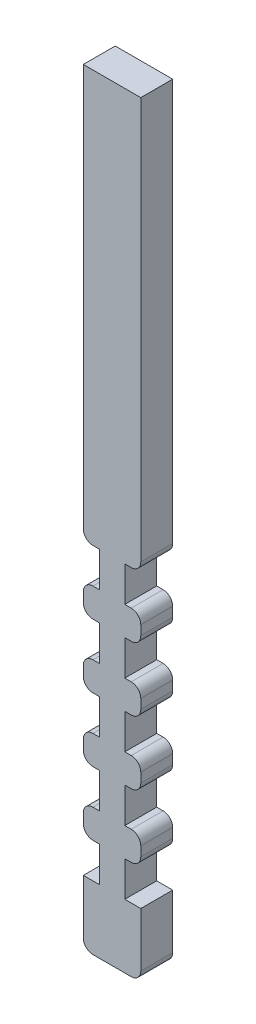
SolidWorks part; units mm, degrees
ref_plane "Front Plane" through (0, 0, 0) normal (0, 0, 1) x (1, 0, 0)
ref_plane "Top Plane" through (0, 0, 0) normal (0, 1, 0) x (1, 0, 0)
ref_plane "Right Plane" through (0, 0, 0) normal (1, 0, 0) x (0, 0, -1)
sketch "Sketch1" plane through (0, 0, 0) normal (0, 0, 1) x (1, 0, 0)
  line L0 (0, 120) -> (0, 0) construction
  line L1 (-9, 0) -> (9, 0)
  line L2 (-9, 0) -> (-9, 120) construction
  line L3 (-9, 120) -> (9, 120) construction
  line L5 (-9, 120) -> (-9, 111)
  line L6 (-9, 111) -> (-3.99, 111)
  line L7 (-3.99, 111) -> (-3.99, 100)
  line L8 (-3.99, 100) -> (-9, 100)
  line L9 (-9, 100) -> (-9, 91)
  line L10 (-9, 91) -> (-3.99, 91)
  line L11 (-3.99, 91) -> (-3.99, 80)
  line L12 (-3.99, 80) -> (-9, 80)
  line L13 (-9, 80) -> (-9, 71)
  line L14 (-9, 71) -> (-3.99, 71)
  line L15 (-3.99, 71) -> (-3.99, 60)
  line L16 (-3.99, 60) -> (-9, 60)
  line L17 (-9, 60) -> (-9, 51)
  line L18 (-9, 51) -> (-3.99, 51)
  line L19 (-3.99, 51) -> (-3.99, 40)
  line L20 (-3.99, 40) -> (-9, 40)
  line L21 (-9, 40) -> (-9, 31)
  line L22 (-9, 31) -> (-3.99, 31)
  line L23 (-3.99, 31) -> (-3.99, 20)
  line L24 (-3.99, 20) -> (-9, 20)
  line L25 (-9, 0) -> (-9, 20)
  line L26 (-9, 120) -> (-3.99, 120)
  line L27 (9, 0) -> (9, 120) construction
  line L28 (9, 120) -> (3.99, 120)
  line L29 (9, 0) -> (9, 20)
  line L30 (3.99, 20) -> (9, 20)
  line L31 (3.99, 31) -> (3.99, 20)
  line L32 (9, 31) -> (3.99, 31)
  line L33 (9, 40) -> (9, 31)
  line L34 (3.99, 40) -> (9, 40)
  line L35 (3.99, 51) -> (3.99, 40)
  line L36 (9, 51) -> (3.99, 51)
  line L37 (9, 60) -> (9, 51)
  line L38 (3.99, 60) -> (9, 60)
  line L39 (3.99, 71) -> (3.99, 60)
  line L40 (9, 71) -> (3.99, 71)
  line L41 (9, 80) -> (9, 71)
  line L42 (3.99, 80) -> (9, 80)
  line L43 (3.99, 91) -> (3.99, 80)
  line L44 (9, 91) -> (3.99, 91)
  line L45 (9, 100) -> (9, 91)
  line L46 (3.99, 100) -> (9, 100)
  line L47 (3.99, 111) -> (3.99, 100)
  line L48 (9, 111) -> (3.99, 111)
  line L49 (9, 120) -> (9, 111)
  line L50 (-3.99, 120) -> (3.99, 120)
  dimension "D1" = 9
  dimension "D2" = 9
  dimension "D3" = 120
  dimension "D4" = 9
  dimension "D5" = 5.01
  dimension "D6" = 11
  dimension "D7" = 9
  dimension "D8" = 9
  dimension "D9" = 11
  dimension "D10" = 9
  dimension "D11" = 11
  dimension "D12" = 9
  dimension "D13" = 11
extrude "Boss-Extrude1" add sketch "Sketch1" along normal blind 10
fillet "Fillet1" radius 3 20 edges at (9, 31, 5) (9, 40, 5) (9, 51, 5) (9, 60, 5) (9, 71, 5) (9, 80, 5) (9, 91, 5) (9, 100, 5) (9, 111, 5) (-9, 111, 5) (-9, 100, 5) (-9, 91, 5) (-9, 80, 5) (-9, 71, 5) (-9, 60, 5) (-9, 51, 5) (-9, 40, 5) (-9, 31, 5) (9, 0, 5) (-9, 0, 5)
sketch "Sketch2" plane through (0, 120, 0) normal (0, 1, 0) x (1, 0, 0)
  line L4 (9, 0) -> (-9, 0)
  line L5 (-9, 0) -> (-9, -10)
  line L6 (-9, -10) -> (9, -10)
  line L7 (9, -10) -> (9, 0)
  line L8 (9, 0) -> (-9, 0)
  line L9 (-9, 0) -> (-9, -10)
  line L10 (-9, -10) -> (9, -10)
  line L11 (9, -10) -> (9, 0)
  dimension "D1" = 0
extrude "Boss-Extrude2" add sketch "Sketch2" along normal blind 120
